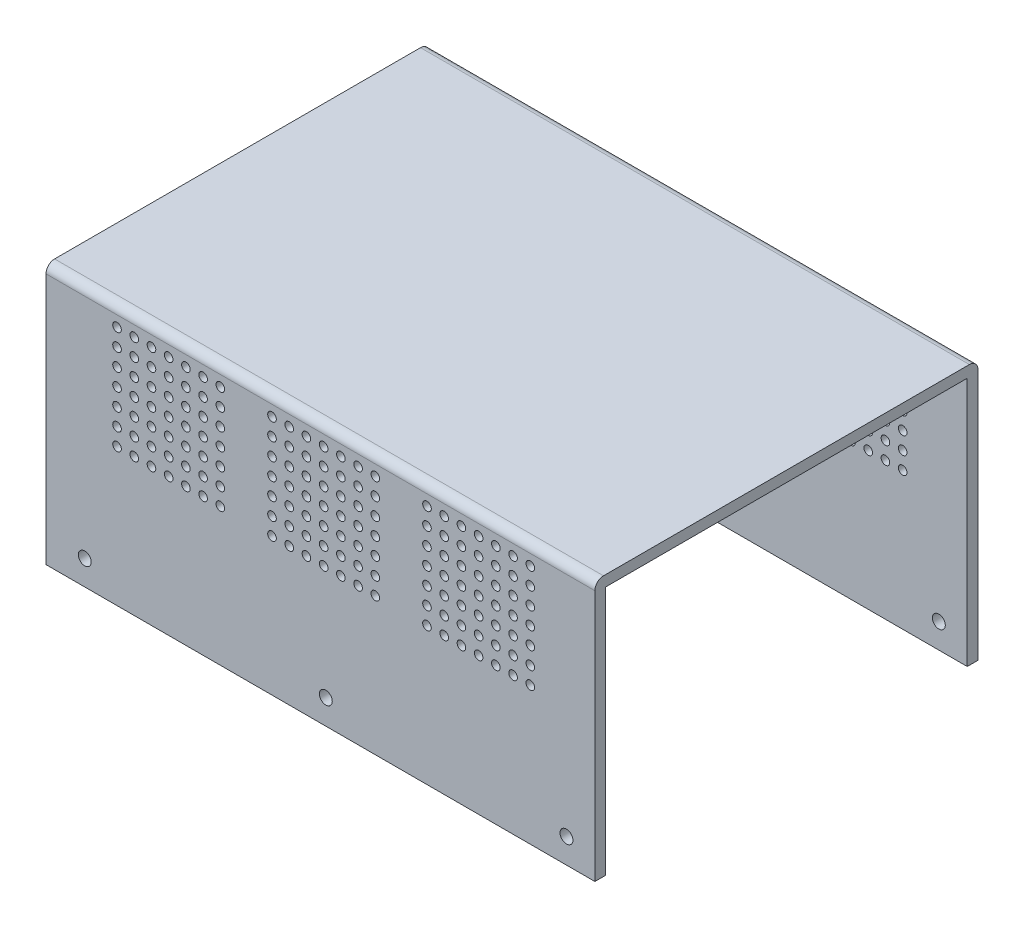
SolidWorks part; units mm, degrees
ref_plane "Front Plane" through (0, 0, 0) normal (0, 0, 1) x (1, 0, 0)
ref_plane "Top Plane" through (0, 0, 0) normal (0, 1, 0) x (1, 0, 0)
ref_plane "Right Plane" through (0, 0, 0) normal (1, 0, 0) x (0, 0, -1)
sketch "Sketch1" plane through (0, 0, 0) normal (1, 0, 0) x (0, 0, -1)
  line L1 (44.5, -30.25) -> (-44.5, -30.25)
  line L2 (44.5, -30.25) -> (44.5, 30.25)
  line L3 (44.5, 30.25) -> (-44.5, 30.25)
  line L4 (-44.5, -30.25) -> (-44.5, 30.25)
  line L5 (44.5, -30.25) -> (-44.5, 30.25) construction
  line L6 (44.5, 30.25) -> (-44.5, -30.25) construction
  point P0 (0, 0)
  dimension "D1" = 89
  dimension "D2" = 60.5
extrude "Boss-Extrude1" add sketch "Sketch1" along normal blind 127.5
shell "Shell1" thickness 2.5
ref_plane "Plane1" through (0, 0, 0) normal (0, 0, -1) x (-1, 0, 0)
sketch "Sketch2" plane through (0, 0, -44.5) normal (0, 0, -1) x (-1, 0, 0)
  line L0 (-127.5, -30.25) -> (0, -30.25) construction
  line L1 (-127.5, -30.25) -> (-127.5, 30.25) construction
  line L2 (0, -30.25) -> (0, 30.25) construction
  circle A0 centre (-120.9, -24.5) radius 1.5
  circle A1 centre (-65, -24.5) radius 1.5
  circle A2 centre (-9, -24.5) radius 1.5
  dimension "D5" = 3
  dimension "D6" = 3
  dimension "D7" = 3
  dimension "D1" = 5.75
  dimension "D2" = 6.6
  dimension "D3" = 62.5
  dimension "D4" = 9
extrude "Cut-Extrude1" cut sketch "Sketch2" against normal up to next
mirror "Mirror1" about plane through (0, 0, 0) normal (0, 0, -1) of "Cut-Extrude1"
sketch "Sketch3" plane through (0, 0, -44.5) normal (0, 0, -1) x (-1, 0, 0)
  line L0 (-127.5, 30.25) -> (0, 30.25) construction
  line L1 (-127.5, -30.25) -> (-127.5, 30.25) construction
  circle A0 centre (-112.5, 25.75) radius 1
  dimension "D1" = 2
  dimension "D2" = 4.5
  dimension "D3" = 15
extrude "Cut-Extrude2" cut sketch "Sketch3" against normal up to next
pattern_linear "LPattern1" count 9 spacing 4 along (0, -1, 0) count 26 spacing 4 along (-1, 0, 0) skipping (0, 7), (0, 8), (0, 16), (0, 17), (0, 25), (1, 7), (1, 8), (1, 16), (1, 17), (1, 25), (2, 7), (2, 8), (2, 16), (2, 17), (2, 25), (3, 7), (3, 8), (3, 16), (3, 17), (3, 25), (4, 7), (4, 8), (4, 16), (4, 17), (4, 25), (5, 7), (5, 8), (5, 16), (5, 17), (5, 25), (6, 7), (6, 8), (6, 16), (6, 17), (6, 25), (7, 0), (7, 1), (7, 2), (7, 3), (7, 4), (7, 5), (7, 6), (7, 7), (7, 8), (7, 9), (7, 10), (7, 11), (7, 12), (7, 13), (7, 14), (7, 15), (7, 16), (7, 17), (7, 18), (7, 19), (7, 20), (7, 21), (7, 22), (7, 23), (7, 24), (7, 25), (8, 0), (8, 1), (8, 2), (8, 3), (8, 4), (8, 5), (8, 6), (8, 7), (8, 8), (8, 9), (8, 10), (8, 11), (8, 12), (8, 13), (8, 14), (8, 15), (8, 16), (8, 17), (8, 18), (8, 19), (8, 20), (8, 21), (8, 22), (8, 23), (8, 24), (8, 25) of "Cut-Extrude2"
ref_plane "Plane2" through (0, 0, 0) normal (0, 0, 1) x (1, 0, 0)
mirror "Mirror2" about plane through (0, 0, 0) normal (0, 0, 1) of "LPattern1", "Cut-Extrude2"
fillet "Fillet2" radius 2 2 edges at (63.75, 30.25, -44.5) (63.75, 30.25, 44.5)
